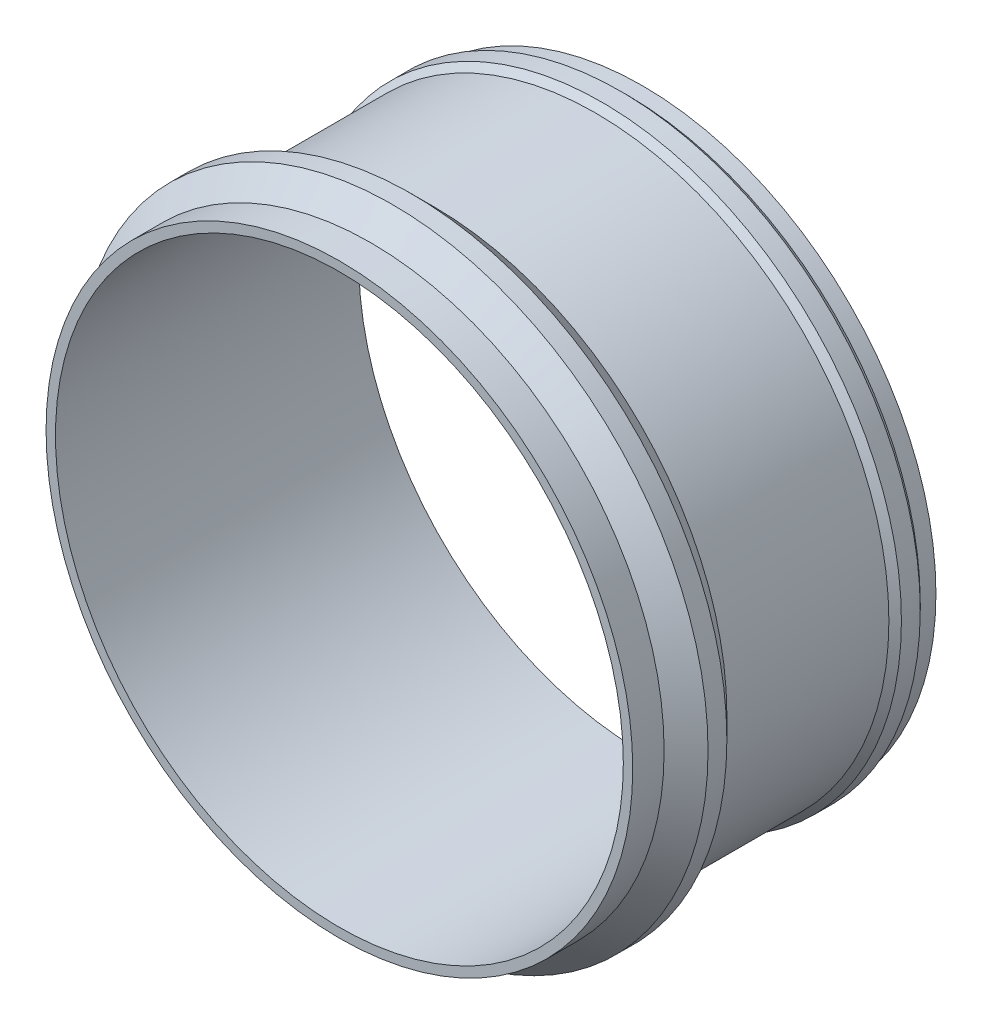
SolidWorks part; units mm, degrees
material "2024 Сплав"
ref_plane "Спереди" through (0, 0, 0) normal (0, 0, 1) x (1, 0, 0)
ref_plane "Сверху" through (0, 0, 0) normal (0, 1, 0) x (1, 0, 0)
ref_plane "Справа" through (0, 0, 0) normal (1, 0, 0) x (0, 0, -1)
sketch "Эскиз1" plane through (0, 0, 0) normal (0, 1, 0) x (1, 0, 0)
  line L0 (0, 0) -> (0, 116.1505) construction
  line L1 (90.5, 120.7467) -> (93.5, 120.7467)
  line L2 (90.5, 120.7467) -> (90.5, 24.1067)
  line L3 (90.5, 24.1067) -> (93.5, 24.1067)
  line L4 (93.5, 120.7467) -> (93.5, 115.7467)
  line L5 (93.5, 24.1067) -> (93.5, 34.1067)
  line L6 (100.5, 41.1067) -> (100.5, 47.1067)
  line L7 (100.5, 47.1067) -> (93.5, 54.1067)
  line L8 (100.5, 41.1067) -> (93.5, 34.1067)
  line L9 (93.5, 115.7467) -> (95.5, 113.7467)
  line L10 (95.5, 113.7467) -> (95.5, 107.7467)
  line L11 (95.5, 107.7467) -> (93.5, 105.7467)
  line L12 (93.5, 105.7467) -> (93.5, 54.1067)
  dimension "D1" = 90.5
  dimension "D2" = 3
  dimension "D3" = 96.64
  dimension "D4" = 10
  dimension "D5" = 45
  dimension "D6" = 20
  dimension "D7" = 45
  dimension "D8" = 10
  dimension "D9" = 5
  dimension "D10" = 45
  dimension "D11" = 10
  dimension "D12" = 5
  dimension "D13" = 45
revolve "Повернуть1" add sketch "Эскиз1" angle 360 about L0
